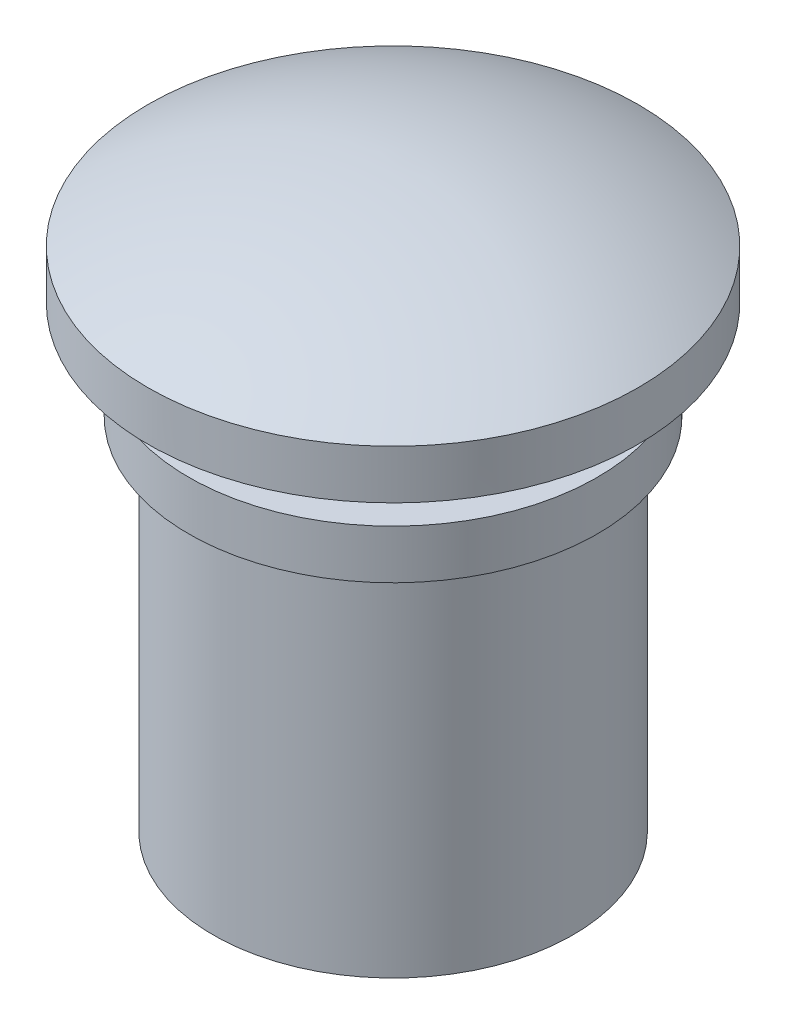
SolidWorks part; units mm, degrees
ref_plane "Front Plane" through (0, 0, 0) normal (0, 0, 1) x (1, 0, 0)
ref_plane "Top Plane" through (0, 0, 0) normal (0, 1, 0) x (1, 0, 0)
ref_plane "Right Plane" through (0, 0, 0) normal (1, 0, 0) x (0, 0, -1)
sketch "Sketch1" plane through (0, 0, 0) normal (1, 0, 0) x (0, 0, -1)
  line L0 (0, 0) -> (0, -22)
  line L1 (0, -22) -> (11, -22)
  line L2 (11, -22) -> (11, 0)
  line L3 (11, 0) -> (12.5, 0)
  line L4 (12.5, 0) -> (12.5, 3)
  line L5 (12.5, 3) -> (8, 3)
  line L6 (8, 3) -> (8, 6)
  line L7 (8, 6) -> (15, 6)
  line L8 (15, 6) -> (15, 9)
  line L9 (0, 0) -> (0, 13)
  arc A0 (0, 13) -> (15, 9) centre (0, -17.125) cw
  point P13 (0, 0)
  dimension "D1" = 22
  dimension "D2" = 11
  dimension "D3" = 12.5
  dimension "D4" = 15
  dimension "D5" = 3
  dimension "D6" = 13
  dimension "D7" = 8
revolve "Revolve1" add sketch "Sketch1" angle 360 about L9
